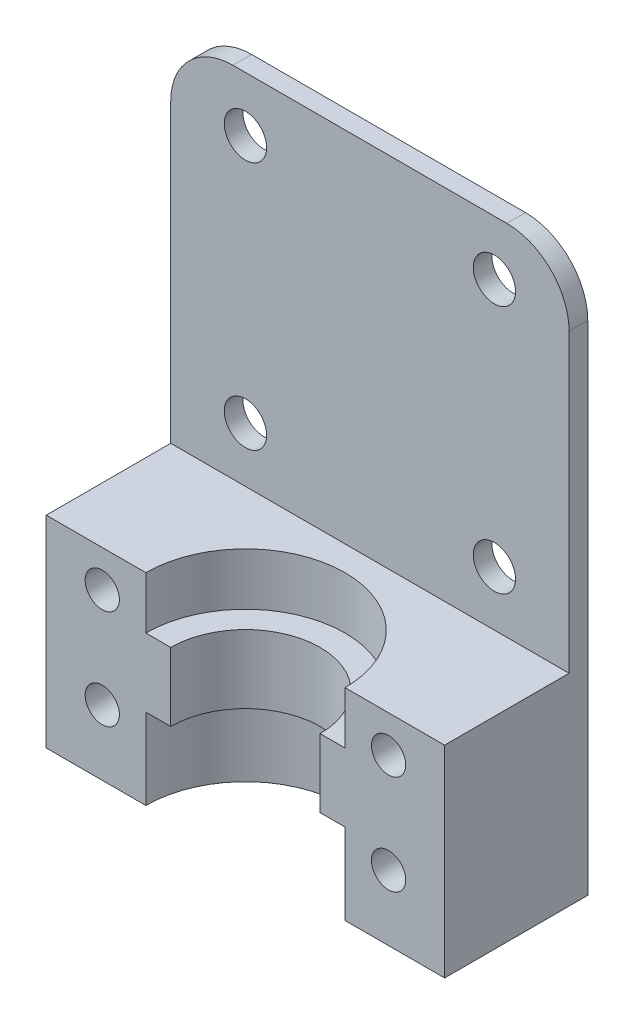
SolidWorks part; units mm, degrees
material "PLA"
ref_plane "Front Plane" through (0, 0, 0) normal (0, 0, 1) x (1, 0, 0)
ref_plane "Top Plane" through (0, 0, 0) normal (0, 1, 0) x (1, 0, 0)
ref_plane "Right Plane" through (0, 0, 0) normal (1, 0, 0) x (0, 0, -1)
sketch "Sketch1" plane through (0, 0, 0) normal (1, 0, 0) x (0, 0, -1)
  line L0 (0, 20) -> (1.5, 20) construction
  line L1 (0, 0) -> (1.5, 0)
  line L2 (0, 0) -> (0, 45)
  line L3 (0, 45) -> (1.5, 45)
  line L4 (1.5, 0) -> (1.5, 45)
  line L5 (0, 5) -> (1.5, 5) construction
  dimension "D1" = 15
  dimension "D2" = 1.5
  dimension "D3" = 45
  dimension "D4" = 5
extrude "Boss-Extrude1" add sketch "Sketch1" along normal mid plane 32 contours L4 L3 L2 L1
sketch "Sketch2" plane through (0, 0, 0) normal (0, 1, 0) x (1, 0, 0)
  line L1 (-16, -10) -> (16, -10)
  line L2 (-16, -10) -> (-16, 0)
  line L3 (-16, 0) -> (16, 0)
  line L4 (16, -10) -> (16, 0)
  line L5 (16, 0) -> (16, 1.5) construction
  dimension "D3" = 10
extrude "Boss-Extrude2" add sketch "Sketch2" along normal blind 16.2
sketch "Sketch9" plane through (0, 0, 0) normal (1, 0, 0) x (0, 0, -1)
  line L0 (-10, 16.2) -> (-2, 16.2)
  line L1 (-10, 16.2) -> (-10, 0) construction
  line L2 (-2, 16.2) -> (-2, 12)
  line L3 (-2, 12) -> (-4, 12)
  line L4 (-4, 12) -> (-4, 6.5)
  line L5 (-4, 6.5) -> (-2, 6.5)
  line L6 (-2, 6.5) -> (-2, 0)
  line L7 (-10, 0) -> (1.5, 0) construction
  line L8 (-2, 0) -> (-10, 0)
  line L9 (-10, 0) -> (-10, 16.2)
  line L10 (-10, 16.2) -> (0, 16.2) construction
  dimension "D1" = 6
  dimension "D2" = 8
  dimension "D3" = 8
  dimension "D4" = 6.5
  dimension "D5" = 5.5
revolve "Cut-Revolve1" cut sketch "Sketch9" angle 360 about L9
hole_wizard "M3x0.5 Tapped Hole1" positions "Sketch12" profile "Sketch11" tap size "M3x0.5" standard "ANSI Metric"
sketch "Sketch12" plane through (0, 0, 10) normal (0, 0, 1) x (1, 0, 0)
  line L0 (0, 0) -> (0, 16.2) construction
  line L1 (8, 16.2) -> (-8, 16.2) construction
  line L4 (-11.5, 13.25) -> (-11.5, 5.25) construction
  line L7 (-11.5, 9.25) -> (0, 9.25) construction
  line L10 (-6, 6.5) -> (-6, 12) construction
  point P0 (-11.5, 13.25)
  point P2 (11.5, 13.25)
  point P7 (-11.5, 5.25)
  point P8 (11.5, 5.25)
  point P36 (-6, 9.25)
  dimension "D1" = 8
  dimension "D2" = 23
sketch "Sketch11" plane through (-11.5, 13.25, 10) normal (1, 0, 0) x (0, -1, 0)
  line L0 (0, 0) -> (0, 12.8262)
  line L1 (0, 12.8262) -> (1.375, 12)
  line L2 (1.375, 12) -> (1.375, 0)
  line L5 (1.375, 0) -> (0, 0)
  line L10 (0, 12.8262) -> (-1.375, 12) construction
  line L11 (0, -6.35) -> (0, 107.95) construction
  dimension "Tap Drill Dia." = 2.75
  dimension "Tap Drill Depth" = 12
  dimension "Drill Angle" = 118
cosmetic thread "Hole Thread7" parameters "D1"=6, "D2"=3
cosmetic thread "Hole Thread8" parameters "D1"=6, "D2"=3
cosmetic thread "Hole Thread9" parameters "D1"=6, "D2"=3
cosmetic thread "Hole Thread10" parameters "D1"=6, "D2"=3
sketch "Sketch13" plane through (0, 0, 0) normal (0, -1, 0) x (1, 0, 0)
  line L0 (-7.375, -1.5) -> (-9.375, -3.5)
  line L1 (16, -1.5) -> (-16, -1.5) construction
  line L2 (-9.375, -3.5) -> (9.375, -3.5)
  line L3 (9.375, -3.5) -> (7.375, -1.5)
  line L4 (7.375, -1.5) -> (-7.375, -1.5)
  line L5 (0, 0) -> (0, -3.5) construction
  dimension "D1" = 14.75
  dimension "D2" = 2
  dimension "D3" = 45
extrude "Boss-Extrude3" add sketch "Sketch13" against normal blind 5
fillet "Fillet1" radius 0.5 4 edges at (7.375, 2.5, -1.5) (9.375, 2.5, -3.5) (-9.375, 2.5, -3.5) (-7.375, 2.5, -1.5)
hole_wizard "M3 Clearance Hole1" positions "Sketch14" profile "Sketch15" hole size "M3" standard "ANSI Metric" end condition through all
sketch "Sketch14" plane through (0, 0, 0) normal (0, 0, 1) x (1, 0, 0)
  line L0 (-10, 40.6) -> (10, 40.6) construction
  line L1 (10, 40.6) -> (10, 20.6) construction
  line L2 (10, 20.6) -> (-10, 20.6) construction
  line L3 (-10, 20.6) -> (-10, 40.6) construction
  line L5 (0, 20.6) -> (0, 0) construction
  line L7 (10, 30.6) -> (16, 30.6) construction
  line L8 (16, 16.2) -> (16, 45) construction
  point P0 (-10, 20.6)
  point P2 (-10, 40.6)
  point P4 (10, 40.6)
  point P6 (10, 20.6)
  dimension "D1" = 20
  dimension "D2" = 20
sketch "Sketch15" plane through (-10, 20.6, 0) normal (1, 0, 0) x (0, -1, 0)
  line L0 (0, 0) -> (0, 3.5)
  line L1 (0, 3.5) -> (1.7, 3.5)
  line L2 (1.7, 3.5) -> (1.7, 0)
  line L5 (1.7, 0) -> (0, 0)
  line L11 (0, -6.35) -> (0, 107.95) construction
  dimension "Thru Hole Dia." = 3.4
  dimension "Thru Hole Depth" = 3.5
fillet "Fillet2" radius 5 2 edges at (-16, 45, -0.75) (16, 45, -0.75)
shell "Shell1" [suppressed] thickness 1.5
